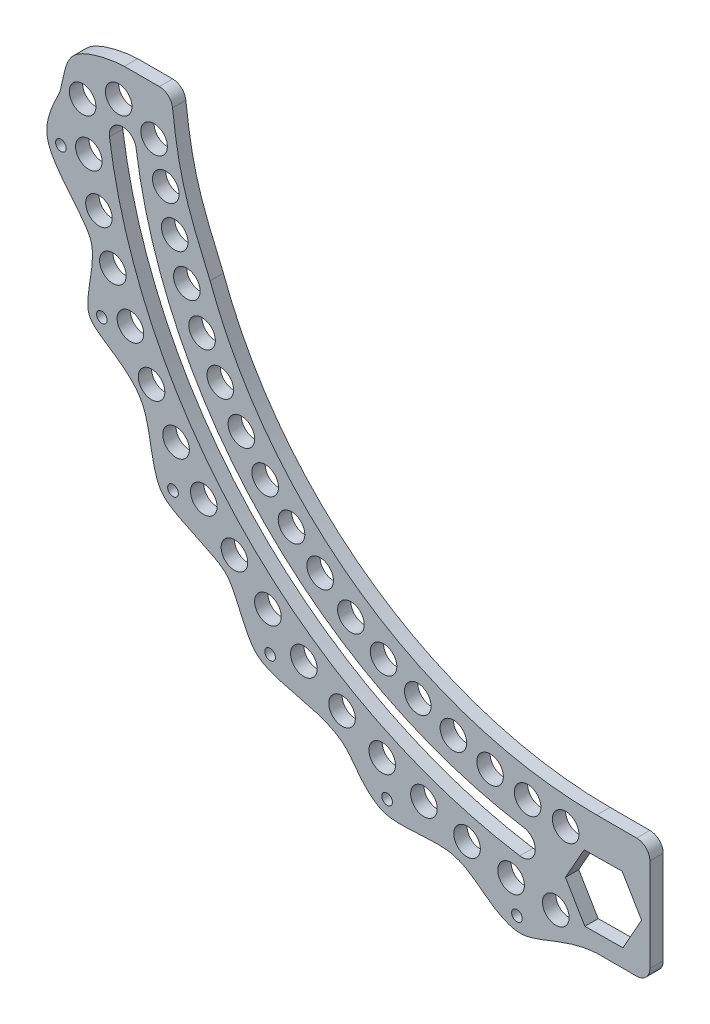
SolidWorks part; units mm, degrees
material "6061-T6 (SS)"
ref_plane "Front Plane" through (0, 0, 0) normal (0, 0, 1) x (1, 0, 0)
ref_plane "Top Plane" through (0, 0, 0) normal (0, 1, 0) x (1, 0, 0)
ref_plane "Right Plane" through (0, 0, 0) normal (1, 0, 0) x (0, 0, -1)
sketch "Layout" plane through (0, 0, 0) normal (0, 0, 1) x (1, 0, 0)
  line L0 (0, 0) -> (-76.2, 0) construction
  line L1 (-76.2, 0) -> (-203.2, 0) construction
  line L2 (-203.2, 0) -> (-254, 0) construction
  dimension "D1" = 76.2
  dimension "D2" = 127
  dimension "D3" = 50.8
sketch "Sketch1" plane through (0, 0, 0) normal (0, 0, 1) x (1, 0, 0)
  line L0 (0, 0) -> (-203.2, 0) construction
  line L1 (0, 0) -> (0, -203.2) construction
  line L2 (0, -203.2) -> (25.4, -203.2)
  line L3 (0, -254) -> (25.4, -254)
  line L4 (-254, 0) -> (-203.2, 0)
  line L5 (25.4, -203.2) -> (25.4, -254)
  arc A0 (-203.2, 0) -> (0, -203.2) centre (0, 0) ccw
  arc A1 (-254, 0) -> (0, -254) centre (0, 0) ccw
  dimension "D1" = 50.8
  dimension "D2" = 25.4
  dimension "D3" = 203.2
extrude "Boss-Extrude1" add sketch "Sketch1" along normal blind 6.35
ref_plane "Mid_Plane" through (0, 0, 3.175) normal (0, 0, 1) x (1, 0, 0)
sketch "Sketch2" plane through (0, 0, 6.35) normal (0, 0, 1) x (1, 0, 0)
  line L0 (0, 0) -> (-229.3095, 0) construction
  line L1 (0, 0) -> (-226.3753, -31.815) construction
  line L2 (0, 0) -> (-35.7609, -225.7856) construction
  arc A0 (-226.3753, -31.815) -> (-35.7609, -225.7856) centre (0, 0) ccw construction
  arc A1 (-226.3753, -31.815) -> (-35.7609, -225.7856) centre (0, 0) ccw construction
  arc A2 (-232.7264, -32.7076) -> (-36.7642, -232.1201) centre (0, 0) ccw
  arc A3 (-220.0242, -30.9224) -> (-34.7576, -219.451) centre (0, 0) ccw
  arc A4 (-220.0242, -30.9224) -> (-232.7264, -32.7076) centre (-226.3753, -31.815) ccw
  arc A5 (-36.7642, -232.1201) -> (-34.7576, -219.451) centre (-35.7609, -225.7856) ccw
  point P5 (-163.0491, -160.2279)
  dimension "D1" = 73
  dimension "D3" = 12.827
  dimension "D4" = 228.6
  dimension "D2" = 8
extrude "Cut-Extrude1" cut sketch "Sketch2" against normal up to next
fillet "Fillet1" [suppressed] radius 12.7
ref_point "Mid_Point"
sketch "Sketch4" plane through (0, 0, 0) normal (0, 0, -1) x (-1, 0, 0)
  line L0 (254, 0) -> (266.7, 0)
  line L1 (0, -254) -> (0, -266.7)
  arc A0 (0, -254) -> (254, 0) centre (0, 0) ccw construction
  arc A1 (0, -254) -> (254, 0) centre (0, 0) ccw
  arc A2 (0, -266.7) -> (266.7, 0) centre (0, 0) ccw
extrude "Boss-Extrude3" add sketch "Sketch4" against normal up to surface (6.35 mm away) up to face at (-145.6981, -143.1771, 6.35)
fillet "Fillet2" radius 12.7 2 edges at (-266.7, 0, 3.175) (0, -266.7, 3.175)
sketch "Sketch5" plane through (0, 0, 0) normal (0, 0, -1) x (-1, 0, 0)
  line L0 (2.758, -261.6055) -> (3.6103, -266.6756)
  line L1 (0, 0) -> (306.4939, -16.1536) construction
  line L2 (0, -261.62) -> (0.7987, -266.6988)
  line L3 (0, -261.62) -> (-1.3603, -266.6965)
  line L4 (2.758, -261.6055) -> (1.4514, -266.6961)
  line L5 (5.5157, -261.5618) -> (6.4214, -266.6227)
  line L6 (5.5157, -261.5618) -> (4.2628, -266.6659)
  line L7 (8.2728, -261.4892) -> (9.2318, -266.5402)
  line L8 (8.2728, -261.4892) -> (7.0738, -266.6062)
  line L9 (11.029, -261.3874) -> (12.0411, -266.428)
  line L10 (11.029, -261.3874) -> (9.884, -266.5168)
  line L11 (13.7839, -261.2566) -> (14.8492, -266.2863)
  line L12 (13.7839, -261.2566) -> (12.693, -266.3978)
  line L13 (16.5374, -261.0968) -> (17.6555, -266.115)
  line L14 (16.5374, -261.0968) -> (15.5007, -266.2492)
  line L15 (19.2889, -260.908) -> (20.46, -265.914)
  line L16 (19.2889, -260.908) -> (18.3067, -266.071)
  line L17 (22.0384, -260.6901) -> (23.2621, -265.6836)
  line L18 (22.0384, -260.6901) -> (21.1106, -265.8632)
  line L19 (24.7854, -260.4433) -> (26.0617, -265.4236)
  line L20 (24.7854, -260.4433) -> (23.9122, -265.6259)
  line L21 (27.5296, -260.1675) -> (28.8583, -265.1341)
  line L22 (27.5296, -260.1675) -> (26.7111, -265.359)
  line L23 (30.2708, -259.8629) -> (31.6518, -264.8151)
  line L24 (30.2708, -259.8629) -> (29.507, -265.0627)
  line L25 (33.0086, -259.5293) -> (34.4417, -264.4667)
  line L26 (33.0086, -259.5293) -> (32.2997, -264.7369)
  line L27 (35.7427, -259.1669) -> (37.2278, -264.089)
  line L28 (35.7427, -259.1669) -> (35.0888, -264.3817)
  line L29 (38.4729, -258.7757) -> (40.0098, -263.6818)
  line L30 (38.4729, -258.7757) -> (37.874, -263.9971)
  line L31 (41.1988, -258.3557) -> (42.7873, -263.2454)
  line L32 (41.1988, -258.3557) -> (40.6549, -263.5831)
  line L33 (43.9201, -257.9071) -> (45.5601, -262.7797)
  line L34 (43.9201, -257.9071) -> (43.4314, -263.1399)
  line L35 (46.6365, -257.4297) -> (48.3278, -262.2848)
  line L36 (46.6365, -257.4297) -> (46.203, -262.6674)
  line L37 (49.3478, -256.9238) -> (51.0902, -261.7607)
  line L38 (49.3478, -256.9238) -> (48.9695, -262.1657)
  line L39 (52.0535, -256.3893) -> (53.8468, -261.2076)
  line L40 (52.0535, -256.3893) -> (51.7305, -261.6349)
  line L41 (54.7535, -255.8263) -> (56.5975, -260.6254)
  line L42 (54.7535, -255.8263) -> (54.4858, -261.0751)
  line L43 (57.4474, -255.2348) -> (59.3419, -260.0143)
  line L44 (57.4474, -255.2348) -> (57.2351, -260.4862)
  line L45 (60.1349, -254.615) -> (62.0797, -259.3743)
  line L46 (60.1349, -254.615) -> (59.978, -259.8683)
  line L47 (62.8157, -253.9669) -> (64.8106, -258.7054)
  line L48 (62.8157, -253.9669) -> (62.7142, -259.2216)
  line L49 (65.4896, -253.2906) -> (67.5342, -258.0078)
  line L50 (65.4896, -253.2906) -> (65.4434, -258.546)
  line L51 (68.1561, -252.5862) -> (70.2504, -257.2815)
  line L52 (68.1561, -252.5862) -> (68.1654, -257.8418)
  line L53 (70.8151, -251.8536) -> (72.9588, -256.5266)
  line L54 (70.8151, -251.8536) -> (70.8798, -257.1088)
  line L55 (73.4663, -251.0931) -> (75.6591, -255.7432)
  line L56 (73.4663, -251.0931) -> (73.5863, -256.3473)
  line L57 (76.1092, -250.3046) -> (78.3509, -254.9314)
  line L58 (76.1092, -250.3046) -> (76.2846, -255.5573)
  line L59 (78.7437, -249.4884) -> (81.0341, -254.0913)
  line L60 (78.7437, -249.4884) -> (78.9745, -254.7389)
  line L61 (81.3695, -248.6444) -> (83.7082, -253.2229)
  line L62 (81.3695, -248.6444) -> (81.6556, -253.8922)
  line L63 (83.9862, -247.7728) -> (86.373, -252.3263)
  line L64 (83.9862, -247.7728) -> (84.3276, -253.0173)
  line L65 (86.5935, -246.8736) -> (89.0283, -251.4018)
  line L66 (86.5935, -246.8736) -> (86.9902, -252.1142)
  line L67 (89.1913, -245.947) -> (91.6736, -250.4493)
  line L68 (89.1913, -245.947) -> (89.6432, -251.1832)
  line L69 (91.7791, -244.9931) -> (94.3088, -249.4689)
  line L70 (91.7791, -244.9931) -> (92.2862, -250.2242)
  line L71 (94.3567, -244.0119) -> (96.9335, -248.4608)
  line L72 (94.3567, -244.0119) -> (94.919, -249.2374)
  line L73 (96.9239, -243.0037) -> (99.5474, -247.4252)
  line L74 (96.9239, -243.0037) -> (97.5412, -248.2229)
  line L75 (99.4803, -241.9684) -> (102.1502, -246.362)
  line L76 (99.4803, -241.9684) -> (100.1525, -247.1808)
  line L77 (102.0256, -240.9062) -> (104.7417, -245.2714)
  line L78 (102.0256, -240.9062) -> (102.7528, -246.1113)
  line L79 (104.5596, -239.8173) -> (107.3215, -244.1536)
  line L80 (104.5596, -239.8173) -> (105.3416, -245.0144)
  line L81 (107.0819, -238.7017) -> (109.8895, -243.0086)
  line L82 (107.0819, -238.7017) -> (107.9187, -243.8902)
  line L83 (109.5924, -237.5595) -> (112.4452, -241.8367)
  line L84 (109.5924, -237.5595) -> (110.4838, -242.739)
  line L85 (112.0907, -236.391) -> (114.9884, -240.6378)
  line L86 (112.0907, -236.391) -> (113.0366, -241.5608)
  line L87 (114.5765, -235.1962) -> (117.5188, -239.4122)
  line L88 (114.5765, -235.1962) -> (115.5769, -240.3557)
  line L89 (117.0496, -233.9753) -> (120.0362, -238.16)
  line L90 (117.0496, -233.9753) -> (118.1043, -239.124)
  line L91 (119.5096, -232.7283) -> (122.5402, -236.8814)
  line L92 (119.5096, -232.7283) -> (120.6186, -237.8656)
  line L93 (121.9564, -231.4555) -> (125.0306, -235.5764)
  line L94 (121.9564, -231.4555) -> (123.1195, -236.5808)
  line L95 (124.3897, -230.157) -> (127.5071, -234.2452)
  line L96 (124.3897, -230.157) -> (125.6067, -235.2697)
  line L97 (126.8091, -228.8329) -> (129.9695, -232.888)
  line L98 (126.8091, -228.8329) -> (128.0799, -233.9325)
  line L99 (129.2144, -227.4833) -> (132.4174, -231.5049)
  line L100 (129.2144, -227.4833) -> (130.539, -232.5693)
  line L101 (131.6054, -226.1085) -> (134.8505, -230.0961)
  line L102 (131.6054, -226.1085) -> (132.9835, -231.1802)
  line L103 (133.9817, -224.7085) -> (137.2687, -228.6617)
  line L104 (133.9817, -224.7085) -> (135.4132, -229.7654)
  line L105 (136.3432, -223.2836) -> (139.6717, -227.2019)
  line L106 (136.3432, -223.2836) -> (137.8279, -228.3251)
  line L107 (138.6895, -221.8339) -> (142.0591, -225.7169)
  line L108 (138.6895, -221.8339) -> (140.2272, -226.8595)
  line L109 (141.0203, -220.3595) -> (144.4307, -224.2067)
  line L110 (141.0203, -220.3595) -> (142.611, -225.3686)
  line L111 (143.3355, -218.8606) -> (146.7863, -222.6717)
  line L112 (143.3355, -218.8606) -> (144.9789, -223.8526)
  line L113 (145.6348, -217.3374) -> (149.1256, -221.1119)
  line L114 (145.6348, -217.3374) -> (147.3307, -222.3118)
  line L115 (147.9179, -215.79) -> (151.4482, -219.5275)
  line L116 (147.9179, -215.79) -> (149.6662, -220.7463)
  line L117 (150.1846, -214.2186) -> (153.7541, -217.9187)
  line L118 (150.1846, -214.2186) -> (151.985, -219.1562)
  line L119 (152.4345, -212.6235) -> (156.0429, -216.2857)
  line L120 (152.4345, -212.6235) -> (154.2869, -217.5418)
  line L121 (154.6675, -211.0047) -> (158.3143, -214.6287)
  line L122 (154.6675, -211.0047) -> (156.5717, -215.9032)
  line L123 (156.8834, -209.3624) -> (160.5681, -212.9478)
  line L124 (156.8834, -209.3624) -> (158.839, -214.2407)
  line L125 (159.0818, -207.6969) -> (162.8041, -211.2432)
  line L126 (159.0818, -207.6969) -> (161.0887, -212.5543)
  line L127 (161.2625, -206.0083) -> (165.022, -209.5152)
  line L128 (161.2625, -206.0083) -> (163.3205, -210.8442)
  line L129 (163.4253, -204.2969) -> (167.2216, -207.7639)
  line L130 (163.4253, -204.2969) -> (165.5342, -209.1108)
  line L131 (165.5699, -202.5627) -> (169.4025, -205.9895)
  line L132 (165.5699, -202.5627) -> (167.7295, -207.3541)
  line L133 (167.6961, -200.806) -> (171.5647, -204.1922)
  line L134 (167.6961, -200.806) -> (169.9061, -205.5744)
  line L135 (169.8037, -199.0269) -> (173.7077, -202.3722)
  line L136 (169.8037, -199.0269) -> (172.0638, -203.7718)
  line L137 (171.8924, -197.2258) -> (175.8315, -200.5297)
  line L138 (171.8924, -197.2258) -> (174.2024, -201.9465)
  line L139 (173.962, -195.4027) -> (177.9357, -198.665)
  line L140 (173.962, -195.4027) -> (176.3217, -200.0989)
  line L141 (176.0123, -193.558) -> (180.0202, -196.7781)
  line L142 (176.0123, -193.558) -> (178.4213, -198.229)
  line L143 (178.043, -191.6917) -> (182.0846, -194.8694)
  line L144 (178.043, -191.6917) -> (180.5012, -196.337)
  line L145 (180.054, -189.8041) -> (184.1288, -192.939)
  line L146 (180.054, -189.8041) -> (182.5609, -194.4232)
  line L147 (182.0449, -187.8954) -> (186.1526, -190.9872)
  line L148 (182.0449, -187.8954) -> (184.6004, -192.4879)
  line L149 (184.0156, -185.9658) -> (188.1556, -189.0141)
  line L150 (184.0156, -185.9658) -> (186.6194, -190.5311)
  line L151 (185.9658, -184.0156) -> (190.1378, -187.0201)
  line L152 (185.9658, -184.0156) -> (188.6176, -188.5532)
  line L153 (187.8954, -182.0449) -> (192.0988, -185.0053)
  line L154 (187.8954, -182.0449) -> (190.5948, -186.5543)
  line L155 (189.8041, -180.054) -> (194.0384, -182.9699)
  line L156 (189.8041, -180.054) -> (192.5509, -184.5346)
  line L157 (191.6917, -178.043) -> (195.9565, -180.9141)
  line L158 (191.6917, -178.043) -> (194.4856, -182.4945)
  line L159 (193.558, -176.0123) -> (197.8529, -178.8383)
  line L160 (193.558, -176.0123) -> (196.3987, -180.4341)
  line L161 (195.4027, -173.962) -> (199.7272, -176.7426)
  line L162 (195.4027, -173.962) -> (198.2899, -178.3536)
  line L163 (197.2258, -171.8924) -> (201.5793, -174.6272)
  line L164 (197.2258, -171.8924) -> (200.1591, -176.2533)
  line L165 (199.0269, -169.8037) -> (203.4091, -172.4925)
  line L166 (199.0269, -169.8037) -> (202.006, -174.1334)
  line L167 (200.806, -167.6961) -> (205.2162, -170.3385)
  line L168 (200.806, -167.6961) -> (203.8305, -171.9942)
  line L169 (202.5627, -165.5699) -> (207.0005, -168.1656)
  line L170 (202.5627, -165.5699) -> (205.6324, -169.8358)
  line L171 (204.2969, -163.4253) -> (208.7618, -165.9741)
  line L172 (204.2969, -163.4253) -> (207.4114, -167.6586)
  line L173 (206.0083, -161.2625) -> (210.4999, -163.7641)
  line L174 (206.0083, -161.2625) -> (209.1673, -165.4628)
  line L175 (207.6969, -159.0818) -> (212.2146, -161.5359)
  line L176 (207.6969, -159.0818) -> (210.9, -163.2485)
  line L177 (209.3624, -156.8834) -> (213.9058, -159.2897)
  line L178 (209.3624, -156.8834) -> (212.6093, -161.0161)
  line L179 (211.0047, -154.6675) -> (215.5731, -157.0259)
  line L180 (211.0047, -154.6675) -> (214.2949, -158.7658)
  line L181 (212.6235, -152.4345) -> (217.2165, -154.7446)
  line L182 (212.6235, -152.4345) -> (215.9567, -156.4979)
  line L183 (214.2186, -150.1846) -> (218.8358, -152.446)
  line L184 (214.2186, -150.1846) -> (217.5945, -154.2126)
  line L185 (215.79, -147.9179) -> (220.4307, -150.1306)
  line L186 (215.79, -147.9179) -> (219.2081, -151.9101)
  line L187 (217.3374, -145.6348) -> (222.0011, -147.7985)
  line L188 (217.3374, -145.6348) -> (220.7974, -149.5908)
  line L189 (218.8606, -143.3355) -> (223.5469, -145.4499)
  line L190 (218.8606, -143.3355) -> (222.3621, -147.2548)
  line L191 (220.3595, -141.0203) -> (225.0678, -143.0852)
  line L192 (220.3595, -141.0203) -> (223.9021, -144.9024)
  line L193 (221.8339, -138.6895) -> (226.5637, -140.7045)
  line L194 (221.8339, -138.6895) -> (225.4173, -142.534)
  line L195 (223.2836, -136.3432) -> (228.0345, -138.3083)
  line L196 (223.2836, -136.3432) -> (226.9074, -140.1497)
  line L197 (224.7085, -133.9817) -> (229.4798, -135.8966)
  line L198 (224.7085, -133.9817) -> (228.3722, -137.7499)
  line L199 (226.1085, -131.6054) -> (230.8997, -133.4699)
  line L200 (226.1085, -131.6054) -> (229.8117, -135.3347)
  line L201 (227.4833, -129.2144) -> (232.2939, -131.0283)
  line L202 (227.4833, -129.2144) -> (231.2256, -132.9045)
  line L203 (228.8329, -126.8091) -> (233.6623, -128.5722)
  line L204 (228.8329, -126.8091) -> (232.6139, -130.4595)
  line L205 (230.157, -124.3897) -> (235.0048, -126.1017)
  line L206 (230.157, -124.3897) -> (233.9762, -128)
  line L207 (231.4555, -121.9564) -> (236.3211, -123.6173)
  line L208 (231.4555, -121.9564) -> (235.3126, -125.5263)
  line L209 (232.7283, -119.5096) -> (237.6111, -121.1191)
  line L210 (232.7283, -119.5096) -> (236.6229, -123.0387)
  line L211 (233.9753, -117.0496) -> (238.8748, -118.6075)
  line L212 (233.9753, -117.0496) -> (237.9068, -120.5373)
  line L213 (235.1962, -114.5765) -> (240.1119, -116.0827)
  line L214 (235.1962, -114.5765) -> (239.1643, -118.0226)
  line L215 (236.391, -112.0907) -> (241.3223, -113.5449)
  line L216 (236.391, -112.0907) -> (240.3952, -115.4948)
  line L217 (237.5595, -109.5924) -> (242.5059, -110.9946)
  line L218 (237.5595, -109.5924) -> (241.5994, -112.9541)
  line L219 (238.7017, -107.0819) -> (243.6625, -108.4319)
  line L220 (238.7017, -107.0819) -> (242.7767, -110.4009)
  line L221 (239.8173, -104.5596) -> (244.792, -105.8572)
  line L222 (239.8173, -104.5596) -> (243.9271, -107.8353)
  line L223 (240.9062, -102.0256) -> (245.8944, -103.2707)
  line L224 (240.9062, -102.0256) -> (245.0503, -105.2579)
  line L225 (241.9684, -99.4803) -> (246.9694, -100.6727)
  line L226 (241.9684, -99.4803) -> (246.1464, -102.6687)
  line L227 (243.0037, -96.9239) -> (248.017, -98.0636)
  line L228 (243.0037, -96.9239) -> (247.215, -100.0681)
  line L229 (244.0119, -94.3567) -> (249.037, -95.4435)
  line L230 (244.0119, -94.3567) -> (248.2562, -97.4564)
  line L231 (244.9931, -91.7791) -> (250.0293, -92.8128)
  line L232 (244.9931, -91.7791) -> (249.2698, -94.8338)
  line L233 (245.947, -89.1913) -> (250.9939, -90.1718)
  line L234 (245.947, -89.1913) -> (250.2557, -92.2007)
  line L235 (246.8736, -86.5935) -> (251.9305, -87.5208)
  line L236 (246.8736, -86.5935) -> (251.2138, -89.5574)
  line L237 (247.7728, -83.9862) -> (252.8392, -84.8601)
  line L238 (247.7728, -83.9862) -> (252.1439, -86.9041)
  line L239 (248.6444, -81.3695) -> (253.7197, -82.1899)
  line L240 (248.6444, -81.3695) -> (253.0461, -84.2412)
  line L241 (249.4884, -78.7437) -> (254.5721, -79.5107)
  line L242 (249.4884, -78.7437) -> (253.9201, -81.5689)
  line L243 (250.3046, -76.1092) -> (255.3961, -76.8225)
  line L244 (250.3046, -76.1092) -> (254.7659, -78.8875)
  line L245 (251.0931, -73.4663) -> (256.1918, -74.1258)
  line L246 (251.0931, -73.4663) -> (255.5834, -76.1973)
  line L247 (251.8536, -70.8151) -> (256.959, -71.4209)
  line L248 (251.8536, -70.8151) -> (256.3724, -73.4987)
  line L249 (252.5862, -68.1561) -> (257.6977, -68.7081)
  line L250 (252.5862, -68.1561) -> (257.133, -70.7919)
  line L251 (253.2906, -65.4896) -> (258.4077, -65.9876)
  line L252 (253.2906, -65.4896) -> (257.865, -68.0773)
  line L253 (253.9669, -62.8157) -> (259.089, -63.2598)
  line L254 (253.9669, -62.8157) -> (258.5684, -65.3551)
  line L255 (254.615, -60.1349) -> (259.7415, -60.5249)
  line L256 (254.615, -60.1349) -> (259.243, -62.6256)
  line L257 (255.2348, -57.4474) -> (260.3651, -57.7834)
  line L258 (255.2348, -57.4474) -> (259.8888, -59.8892)
  line L259 (255.8263, -54.7535) -> (260.9598, -55.0354)
  line L260 (255.8263, -54.7535) -> (260.5057, -57.1461)
  line L261 (256.3893, -52.0535) -> (261.5254, -52.2813)
  line L262 (256.3893, -52.0535) -> (261.0937, -54.3966)
  line L263 (256.9238, -49.3478) -> (262.0621, -49.5213)
  line L264 (256.9238, -49.3478) -> (261.6526, -51.6412)
  line L265 (257.4297, -46.6365) -> (262.5696, -46.7559)
  line L266 (257.4297, -46.6365) -> (262.1825, -48.8799)
  line L267 (257.9071, -43.9201) -> (263.0479, -43.9853)
  line L268 (257.9071, -43.9201) -> (262.6832, -46.1133)
  line L269 (258.3557, -41.1988) -> (263.497, -41.2098)
  line L270 (258.3557, -41.1988) -> (263.1547, -43.3415)
  line L271 (258.7757, -38.4729) -> (263.9167, -38.4297)
  line L272 (258.7757, -38.4729) -> (263.597, -40.5649)
  line L273 (259.1669, -35.7427) -> (264.3072, -35.6453)
  line L274 (259.1669, -35.7427) -> (264.01, -37.7838)
  line L275 (259.5293, -33.0086) -> (264.6683, -32.857)
  line L276 (259.5293, -33.0086) -> (264.3936, -34.9985)
  line L277 (259.8629, -30.2708) -> (265, -30.065)
  line L278 (259.8629, -30.2708) -> (264.7479, -32.2093)
  line L279 (260.1675, -27.5296) -> (265.3022, -27.2697)
  line L280 (260.1675, -27.5296) -> (265.0727, -29.4165)
  line L281 (260.4433, -24.7854) -> (265.5749, -24.4714)
  line L282 (260.4433, -24.7854) -> (265.3681, -26.6204)
  line L283 (260.6901, -22.0384) -> (265.8181, -21.6703)
  line L284 (260.6901, -22.0384) -> (265.634, -23.8214)
  line L285 (260.908, -19.2889) -> (266.0318, -18.8668)
  line L286 (260.908, -19.2889) -> (265.8704, -21.0198)
  line L287 (261.0968, -16.5374) -> (266.2159, -16.0612)
  line L288 (261.0968, -16.5374) -> (266.0772, -18.2158)
  line L289 (261.2566, -13.7839) -> (266.3705, -13.2539)
  line L290 (261.2566, -13.7839) -> (266.2544, -15.4098)
  line L291 (261.3874, -11.029) -> (266.4954, -10.4451)
  line L292 (261.3874, -11.029) -> (266.4021, -12.602)
  line L301 (0, 0) -> (0, -261.62) construction
  arc A0 (13.3308, -266.3666) -> (266.3664, -13.335) centre (0, 0) ccw construction
  arc A1 (-1.3603, -266.6965) -> (0.7987, -266.6988) centre (0, 0) ccw
  arc A2 (1.4514, -266.6961) -> (3.6103, -266.6756) centre (0, 0) ccw
  arc A3 (4.2628, -266.6659) -> (6.4214, -266.6227) centre (0, 0) ccw
  arc A4 (7.0738, -266.6062) -> (9.2318, -266.5402) centre (0, 0) ccw
  arc A5 (9.884, -266.5168) -> (12.0411, -266.428) centre (0, 0) ccw
  arc A6 (12.693, -266.3978) -> (14.8492, -266.2863) centre (0, 0) ccw
  arc A7 (15.5007, -266.2492) -> (17.6555, -266.115) centre (0, 0) ccw
  arc A8 (18.3067, -266.071) -> (20.46, -265.914) centre (0, 0) ccw
  arc A9 (21.1106, -265.8632) -> (23.2621, -265.6836) centre (0, 0) ccw
  arc A10 (23.9122, -265.6259) -> (26.0617, -265.4236) centre (0, 0) ccw
  arc A11 (26.7111, -265.359) -> (28.8583, -265.1341) centre (0, 0) ccw
  arc A12 (29.507, -265.0627) -> (31.6518, -264.8151) centre (0, 0) ccw
  arc A13 (32.2997, -264.7369) -> (34.4417, -264.4667) centre (0, 0) ccw
  arc A14 (35.0888, -264.3817) -> (37.2278, -264.089) centre (0, 0) ccw
  arc A15 (37.874, -263.9971) -> (40.0098, -263.6818) centre (0, 0) ccw
  arc A16 (40.6549, -263.5831) -> (42.7873, -263.2454) centre (0, 0) ccw
  arc A17 (43.4314, -263.1399) -> (45.5601, -262.7797) centre (0, 0) ccw
  arc A18 (46.203, -262.6674) -> (48.3278, -262.2848) centre (0, 0) ccw
  arc A19 (48.9695, -262.1657) -> (51.0902, -261.7607) centre (0, 0) ccw
  arc A20 (51.7305, -261.6349) -> (53.8468, -261.2076) centre (0, 0) ccw
  arc A21 (54.4858, -261.0751) -> (56.5975, -260.6254) centre (0, 0) ccw
  arc A22 (57.2351, -260.4862) -> (59.3419, -260.0143) centre (0, 0) ccw
  arc A23 (59.978, -259.8683) -> (62.0797, -259.3743) centre (0, 0) ccw
  arc A24 (62.7142, -259.2216) -> (64.8106, -258.7054) centre (0, 0) ccw
  arc A25 (65.4434, -258.546) -> (67.5342, -258.0078) centre (0, 0) ccw
  arc A26 (68.1654, -257.8418) -> (70.2504, -257.2815) centre (0, 0) ccw
  arc A27 (70.8798, -257.1088) -> (72.9588, -256.5266) centre (0, 0) ccw
  arc A28 (73.5863, -256.3473) -> (75.6591, -255.7432) centre (0, 0) ccw
  arc A29 (76.2846, -255.5573) -> (78.3509, -254.9314) centre (0, 0) ccw
  arc A30 (78.9745, -254.7389) -> (81.0341, -254.0913) centre (0, 0) ccw
  arc A31 (81.6556, -253.8922) -> (83.7082, -253.2229) centre (0, 0) ccw
  arc A32 (84.3276, -253.0173) -> (86.373, -252.3263) centre (0, 0) ccw
  arc A33 (86.9902, -252.1142) -> (89.0283, -251.4018) centre (0, 0) ccw
  arc A34 (89.6432, -251.1832) -> (91.6736, -250.4493) centre (0, 0) ccw
  arc A35 (92.2862, -250.2242) -> (94.3088, -249.4689) centre (0, 0) ccw
  arc A36 (94.919, -249.2374) -> (96.9335, -248.4608) centre (0, 0) ccw
  arc A37 (97.5412, -248.2229) -> (99.5474, -247.4252) centre (0, 0) ccw
  arc A38 (100.1525, -247.1808) -> (102.1502, -246.362) centre (0, 0) ccw
  arc A39 (102.7528, -246.1113) -> (104.7417, -245.2714) centre (0, 0) ccw
  arc A40 (105.3416, -245.0144) -> (107.3215, -244.1536) centre (0, 0) ccw
  arc A41 (107.9187, -243.8902) -> (109.8895, -243.0086) centre (0, 0) ccw
  arc A42 (110.4838, -242.739) -> (112.4452, -241.8367) centre (0, 0) ccw
  arc A43 (113.0366, -241.5608) -> (114.9884, -240.6378) centre (0, 0) ccw
  arc A44 (115.5769, -240.3557) -> (117.5188, -239.4122) centre (0, 0) ccw
  arc A45 (118.1043, -239.124) -> (120.0362, -238.16) centre (0, 0) ccw
  arc A46 (120.6186, -237.8656) -> (122.5402, -236.8814) centre (0, 0) ccw
  arc A47 (123.1195, -236.5808) -> (125.0306, -235.5764) centre (0, 0) ccw
  arc A48 (125.6067, -235.2697) -> (127.5071, -234.2452) centre (0, 0) ccw
  arc A49 (128.0799, -233.9325) -> (129.9695, -232.888) centre (0, 0) ccw
  arc A50 (130.539, -232.5693) -> (132.4174, -231.5049) centre (0, 0) ccw
  arc A51 (132.9835, -231.1802) -> (134.8505, -230.0961) centre (0, 0) ccw
  arc A52 (135.4132, -229.7654) -> (137.2687, -228.6617) centre (0, 0) ccw
  arc A53 (137.8279, -228.3251) -> (139.6717, -227.2019) centre (0, 0) ccw
  arc A54 (140.2272, -226.8595) -> (142.0591, -225.7169) centre (0, 0) ccw
  arc A55 (142.611, -225.3686) -> (144.4307, -224.2067) centre (0, 0) ccw
  arc A56 (144.9789, -223.8526) -> (146.7863, -222.6717) centre (0, 0) ccw
  arc A57 (147.3307, -222.3118) -> (149.1256, -221.1119) centre (0, 0) ccw
  arc A58 (149.6662, -220.7463) -> (151.4482, -219.5275) centre (0, 0) ccw
  arc A59 (151.985, -219.1562) -> (153.7541, -217.9187) centre (0, 0) ccw
  arc A60 (154.2869, -217.5418) -> (156.0429, -216.2857) centre (0, 0) ccw
  arc A61 (156.5717, -215.9032) -> (158.3143, -214.6287) centre (0, 0) ccw
  arc A62 (158.839, -214.2407) -> (160.5681, -212.9478) centre (0, 0) ccw
  arc A63 (161.0887, -212.5543) -> (162.8041, -211.2432) centre (0, 0) ccw
  arc A64 (163.3205, -210.8442) -> (165.022, -209.5152) centre (0, 0) ccw
  arc A65 (165.5342, -209.1108) -> (167.2216, -207.7639) centre (0, 0) ccw
  arc A66 (167.7295, -207.3541) -> (169.4025, -205.9895) centre (0, 0) ccw
  arc A67 (169.9061, -205.5744) -> (171.5647, -204.1922) centre (0, 0) ccw
  arc A68 (172.0638, -203.7718) -> (173.7077, -202.3722) centre (0, 0) ccw
  arc A69 (174.2024, -201.9465) -> (175.8315, -200.5297) centre (0, 0) ccw
  arc A70 (176.3217, -200.0989) -> (177.9357, -198.665) centre (0, 0) ccw
  arc A71 (178.4213, -198.229) -> (180.0202, -196.7781) centre (0, 0) ccw
  arc A72 (180.5012, -196.337) -> (182.0846, -194.8694) centre (0, 0) ccw
  arc A73 (182.5609, -194.4232) -> (184.1288, -192.939) centre (0, 0) ccw
  arc A74 (184.6004, -192.4879) -> (186.1526, -190.9872) centre (0, 0) ccw
  arc A75 (186.6194, -190.5311) -> (188.1556, -189.0141) centre (0, 0) ccw
  arc A76 (188.6176, -188.5532) -> (190.1378, -187.0201) centre (0, 0) ccw
  arc A77 (190.5948, -186.5543) -> (192.0988, -185.0053) centre (0, 0) ccw
  arc A78 (192.5509, -184.5346) -> (194.0384, -182.9699) centre (0, 0) ccw
  arc A79 (194.4856, -182.4945) -> (195.9565, -180.9141) centre (0, 0) ccw
  arc A80 (196.3987, -180.4341) -> (197.8529, -178.8383) centre (0, 0) ccw
  arc A81 (198.2899, -178.3536) -> (199.7272, -176.7426) centre (0, 0) ccw
  arc A82 (200.1591, -176.2533) -> (201.5793, -174.6272) centre (0, 0) ccw
  arc A83 (202.006, -174.1334) -> (203.4091, -172.4925) centre (0, 0) ccw
  arc A84 (203.8305, -171.9942) -> (205.2162, -170.3385) centre (0, 0) ccw
  arc A85 (205.6324, -169.8358) -> (207.0005, -168.1656) centre (0, 0) ccw
  arc A86 (207.4114, -167.6586) -> (208.7618, -165.9741) centre (0, 0) ccw
  arc A87 (209.1673, -165.4628) -> (210.4999, -163.7641) centre (0, 0) ccw
  arc A88 (210.9, -163.2485) -> (212.2146, -161.5359) centre (0, 0) ccw
  arc A89 (212.6093, -161.0161) -> (213.9058, -159.2897) centre (0, 0) ccw
  arc A90 (214.2949, -158.7658) -> (215.5731, -157.0259) centre (0, 0) ccw
  arc A91 (215.9567, -156.4979) -> (217.2165, -154.7446) centre (0, 0) ccw
  arc A92 (217.5945, -154.2126) -> (218.8358, -152.446) centre (0, 0) ccw
  arc A93 (219.2081, -151.9101) -> (220.4307, -150.1306) centre (0, 0) ccw
  arc A94 (220.7974, -149.5908) -> (222.0011, -147.7985) centre (0, 0) ccw
  arc A95 (222.3621, -147.2548) -> (223.5469, -145.4499) centre (0, 0) ccw
  arc A96 (223.9021, -144.9024) -> (225.0678, -143.0852) centre (0, 0) ccw
  arc A97 (225.4173, -142.534) -> (226.5637, -140.7045) centre (0, 0) ccw
  arc A98 (226.9074, -140.1497) -> (228.0345, -138.3083) centre (0, 0) ccw
  arc A99 (228.3722, -137.7499) -> (229.4798, -135.8966) centre (0, 0) ccw
  arc A100 (229.8117, -135.3347) -> (230.8997, -133.4699) centre (0, 0) ccw
  arc A101 (231.2256, -132.9045) -> (232.2939, -131.0283) centre (0, 0) ccw
  arc A102 (232.6139, -130.4595) -> (233.6623, -128.5722) centre (0, 0) ccw
  arc A103 (233.9762, -128) -> (235.0048, -126.1017) centre (0, 0) ccw
  arc A104 (235.3126, -125.5263) -> (236.3211, -123.6173) centre (0, 0) ccw
  arc A105 (236.6229, -123.0387) -> (237.6111, -121.1191) centre (0, 0) ccw
  arc A106 (237.9068, -120.5373) -> (238.8748, -118.6075) centre (0, 0) ccw
  arc A107 (239.1643, -118.0226) -> (240.1119, -116.0827) centre (0, 0) ccw
  arc A108 (240.3952, -115.4948) -> (241.3223, -113.5449) centre (0, 0) ccw
  arc A109 (241.5994, -112.9541) -> (242.5059, -110.9946) centre (0, 0) ccw
  arc A110 (242.7767, -110.4009) -> (243.6625, -108.4319) centre (0, 0) ccw
  arc A111 (243.9271, -107.8353) -> (244.792, -105.8572) centre (0, 0) ccw
  arc A112 (245.0503, -105.2579) -> (245.8944, -103.2707) centre (0, 0) ccw
  arc A113 (246.1464, -102.6687) -> (246.9694, -100.6727) centre (0, 0) ccw
  arc A114 (247.215, -100.0681) -> (248.017, -98.0636) centre (0, 0) ccw
  arc A115 (248.2562, -97.4564) -> (249.037, -95.4435) centre (0, 0) ccw
  arc A116 (249.2698, -94.8338) -> (250.0293, -92.8128) centre (0, 0) ccw
  arc A117 (250.2557, -92.2007) -> (250.9939, -90.1718) centre (0, 0) ccw
  arc A118 (251.2138, -89.5574) -> (251.9305, -87.5208) centre (0, 0) ccw
  arc A119 (252.1439, -86.9041) -> (252.8392, -84.8601) centre (0, 0) ccw
  arc A120 (253.0461, -84.2412) -> (253.7197, -82.1899) centre (0, 0) ccw
  arc A121 (253.9201, -81.5689) -> (254.5721, -79.5107) centre (0, 0) ccw
  arc A122 (254.7659, -78.8875) -> (255.3961, -76.8225) centre (0, 0) ccw
  arc A123 (255.5834, -76.1973) -> (256.1918, -74.1258) centre (0, 0) ccw
  arc A124 (256.3724, -73.4987) -> (256.959, -71.4209) centre (0, 0) ccw
  arc A125 (257.133, -70.7919) -> (257.6977, -68.7081) centre (0, 0) ccw
  arc A126 (257.865, -68.0773) -> (258.4077, -65.9876) centre (0, 0) ccw
  arc A127 (258.5684, -65.3551) -> (259.089, -63.2598) centre (0, 0) ccw
  arc A128 (259.243, -62.6256) -> (259.7415, -60.5249) centre (0, 0) ccw
  arc A129 (259.8888, -59.8892) -> (260.3651, -57.7834) centre (0, 0) ccw
  arc A130 (260.5057, -57.1461) -> (260.9598, -55.0354) centre (0, 0) ccw
  arc A131 (261.0937, -54.3966) -> (261.5254, -52.2813) centre (0, 0) ccw
  arc A132 (261.6526, -51.6412) -> (262.0621, -49.5213) centre (0, 0) ccw
  arc A133 (262.1825, -48.8799) -> (262.5696, -46.7559) centre (0, 0) ccw
  arc A134 (262.6832, -46.1133) -> (263.0479, -43.9853) centre (0, 0) ccw
  arc A135 (263.1547, -43.3415) -> (263.497, -41.2098) centre (0, 0) ccw
  arc A136 (263.597, -40.5649) -> (263.9167, -38.4297) centre (0, 0) ccw
  arc A137 (264.01, -37.7838) -> (264.3072, -35.6453) centre (0, 0) ccw
  arc A138 (264.3936, -34.9985) -> (264.6683, -32.857) centre (0, 0) ccw
  arc A139 (264.7479, -32.2093) -> (265, -30.065) centre (0, 0) ccw
  arc A140 (265.0727, -29.4165) -> (265.3022, -27.2697) centre (0, 0) ccw
  arc A141 (265.3681, -26.6204) -> (265.5749, -24.4714) centre (0, 0) ccw
  arc A142 (265.634, -23.8214) -> (265.8181, -21.6703) centre (0, 0) ccw
  arc A143 (265.8704, -21.0198) -> (266.0318, -18.8668) centre (0, 0) ccw
  arc A144 (266.0772, -18.2158) -> (266.2159, -16.0612) centre (0, 0) ccw
  arc A145 (266.2544, -15.4098) -> (266.3705, -13.2539) centre (0, 0) ccw
  arc A146 (266.4021, -12.602) -> (266.4954, -10.4451) centre (0, 0) ccw
  dimension "D1" = 2.159
  dimension "D2" = 146
  dimension "D4" = 261.62
extrude "Cut-Extrude2" [suppressed] cut sketch "Sketch5" against normal up to surface (6.35 mm away)
sketch "Sketch6" plane through (0, 0, 6.35) normal (0, 0, 1) x (1, 0, 0)
  line L0 (0, 0) -> (-202.3753, -163.7976) construction
  circle A1 centre (-255.9253, -47.8297) radius 2.54
  circle A2 centre (-236.3726, -109.1487) radius 2.54
  circle A3 centre (-202.3753, -163.7976) radius 2.54
  circle A4 centre (-156.0111, -208.437) radius 2.54
  circle A5 centre (-100.1131, -240.3389) radius 2.54
  circle A6 centre (-38.0972, -257.5539) radius 2.54
  point P15 (0, 0)
  dimension "D1" = 6
extrude "Cut-Extrude3" cut sketch "Sketch6" against normal through all
sketch "Sketch9" plane through (0, 0, 6.35) normal (0, 0, 1) x (1, 0, 0)
  line L0 (25.4, -203.2) -> (0, -203.2) construction
  line L1 (25.4, -203.2) -> (0, -203.2)
  line L2 (25.4, -196.85) -> (0, -196.85)
  line L3 (25.4, -203.2) -> (25.4, -196.85)
  arc A1 (-203.2, 0) -> (0, -203.2) centre (0, 0) ccw construction
  arc A2 (-203.2, 0) -> (0, -203.2) centre (0, 0) ccw
  arc A3 (-184.643, -68.2412) -> (0, -196.85) centre (0, 0) ccw
  arc A4 (-196.85, 0) -> (0, -196.85) centre (0, 0) ccw construction
  spline S0 degree 3 poles (-203.2, 0) (-199.8847, -32.721) (-195.8268, -42.2466) (-184.643, -68.2412) knots 0 0 0 0 1 1 1 1
  dimension "D1" = 6.35
extrude "Boss-Extrude4" add sketch "Sketch9" against normal up to surface (6.35 mm away)
sketch "Sketch10" plane through (0, 0, 0) normal (0, 0, -1) x (-1, 0, 0)
  line L0 (0, 0) -> (14.8412, -209.1023) construction
  line L1 (0, 0) -> (33.0092, -207.0131) construction
  line L2 (0, 0) -> (19.5425, -245.8839) construction
  line L3 (0, 0) -> (40.8983, -243.245) construction
  circle A0 centre (0, 0) radius 209.6283 construction
  circle A1 centre (14.8412, -209.1023) radius 6.35
  circle A2 centre (33.0092, -207.0131) radius 6.35
  circle A3 centre (50.9259, -203.3484) radius 6.35
  circle A4 centre (68.4551, -198.1361) radius 6.35
  circle A5 centre (85.4633, -191.4159) radius 6.35
  circle A6 centre (101.8211, -183.2389) radius 6.35
  circle A7 centre (117.404, -173.6673) radius 6.35
  circle A8 centre (0, 0) radius 246.6593 construction
  circle A9 centre (19.5425, -245.8839) radius 6.35
  circle A10 centre (40.8983, -243.245) radius 6.35
  circle A11 centre (61.9429, -238.7548) radius 6.35
  circle A12 centre (82.516, -232.4476) radius 6.35
  circle A13 centre (102.4612, -224.3714) radius 6.35
  circle A14 centre (121.6265, -214.5875) radius 6.35
  circle A15 centre (139.8662, -203.1705) radius 6.35
  circle A16 centre (157.0415, -190.2072) radius 6.35
  circle A17 centre (173.0215, -175.7963) radius 6.35
  circle A18 centre (187.6848, -160.0475) radius 6.35
  circle A19 centre (200.9196, -143.0807) radius 6.35
  circle A20 centre (212.6254, -125.0249) radius 6.35
  circle A21 centre (222.7129, -106.0177) radius 6.35
  circle A22 centre (231.1055, -86.2035) radius 6.35
  circle A23 centre (237.7392, -65.7333) radius 6.35
  circle A24 centre (242.5636, -44.7628) radius 6.35
  circle A25 centre (245.5419, -23.4517) radius 6.35
  circle A26 centre (132.0933, -162.774) radius 6.35
  circle A27 centre (145.7774, -150.6419) radius 6.35
  circle A28 centre (158.3519, -137.3633) radius 6.35
  circle A29 centre (169.7214, -123.0393) radius 6.35
  circle A30 centre (179.7991, -107.7789) radius 6.35
  circle A31 centre (188.5085, -91.6983) radius 6.35
  circle A32 centre (195.7832, -74.9197) radius 6.35
  circle A33 centre (201.5678, -57.571) radius 6.35
  circle A34 centre (205.8185, -39.7842) radius 6.35
  dimension "D1" = 16
  dimension "D3" = 12.7
  dimension "D2" = 5
  dimension "D5" = 5
  dimension "D4" = 17
extrude "Cut-Extrude4" cut sketch "Sketch10" against normal through all
fillet "Fillet4" radius 6.35 3 edges at (25.4, -196.85, 3.175) (25.4, -254, 3.175) (-203.2, 0, 3.175)
sketch "Sketch11" plane through (0, 0, 0) normal (0, 0, -1) x (-1, 0, 0)
  line L0 (208.9049, 0) -> (253.6823, 0) construction
  line L1 (0, -254) -> (-20.604, -275.1109)
  line L2 (-20.604, -275.1109) -> (41.8211, -336.0374)
  line L3 (41.8211, -336.0374) -> (294.3655, -150.7225)
  line L4 (294.3655, -150.7225) -> (308.3021, 25.4576)
  line L5 (308.3021, 25.4576) -> (229.7845, 31.6687)
  line L6 (229.7845, 31.6687) -> (225.6439, 0)
  arc A0 (13.3308, -266.3666) -> (266.3664, -13.335) centre (0, 0) ccw construction
  spline S0 degree 3 poles (0, -254) (15.2893, -255.0418) (30.1751, -265.8271) (49.8532, -261.6268) (58.4804, -250.4001) (76.1235, -245.4444) (97.3175, -249.4675) (113.6752, -239.9773) (116.169, -230.1859) (133.8136, -219.9908) (152.8493, -218.0534) (167.5522, -208.5111) (172.2887, -189.6062) (183.029, -180.2088) (203.9614, -172.8786) (213.0333, -159.7938) (212.9368, -140.7119) (224.5477, -123.5135) (240.0721, -116.7742) (244.9974, -105.552) (238.7607, -87.4313) (244.4381, -72.4105) (260.0839, -57.9116) (263.953, -41.6393) (258.9025, -31.1782) (254.8765, -23.0552) (254.4572, -11.5116) (243.7099, -2.252) (230.6571, -0.0871) (225.6439, 0) knots 0 0 0 0 0.030478 0.038498 0.075567 0.083957 0.114007 0.124448 0.177917 0.191851 0.24985 0.263325 0.313129 0.325531 0.374939 0.389639 0.457828 0.475757 0.550995 0.571534 0.66061 0.681965 0.763729 0.781255 0.839705 0.854441 0.913881 0.92918 1 1 1 1
extrude "Cut-Extrude5" cut sketch "Sketch11" against normal through all
sketch "Sketch12" plane through (0, 0, 0) normal (0, 0, -1) x (-1, 0, 0)
  line L1 (6.0298, -214.2524) -> (-12.1423, -214.0367)
  line L2 (-12.1423, -214.0367) -> (-21.4151, -229.6663)
  line L3 (-21.4151, -229.6663) -> (-12.5158, -245.5115)
  line L4 (-12.5158, -245.5115) -> (5.6562, -245.7272)
  line L5 (5.6562, -245.7272) -> (14.929, -230.0976)
  line L6 (14.929, -230.0976) -> (6.0298, -214.2524)
  circle A0 centre (-3.243, -229.8819) radius 15.7385 construction
  circle A1 centre (211.4229, -22.914) radius 6.35
  circle A2 centre (228.3389, -14.8648) radius 6.35
extrude "Cut-Extrude6" cut sketch "Sketch12" against normal through all
sketch "Sketch13" plane through (0, 0, 0) normal (0, 0, -1) x (-1, 0, 0)
  line L0 (38.6175, -263.8893) -> (39.4953, -270.1784) construction
  line L1 (35.4262, -263.9934) -> (36.3507, -270.6173)
  line L2 (41.7218, -263.1624) -> (42.6398, -269.7395)
  line L3 (242.1767, -111.7109) -> (247.8982, -114.4654) construction
  line L4 (217.2744, 0) -> (217.2744, 6.35) construction
  line L5 (220.4494, 0) -> (220.4494, 6.35)
  line L6 (-19.05, -254) -> (0, -254)
  line L7 (102.4988, -246.2172) -> (102.5589, -246.1921)
  line L8 (207.4638, -167.5938) -> (207.4849, -167.5677)
  line L9 (225.6439, 0) -> (208.9049, 0)
  line L10 (0, -196.85) -> (-19.05, -196.85)
  line L11 (-25.4, -203.2) -> (-25.4, -247.65)
  line L12 (-19.05, -254) -> (0, -254)
  line L13 (102.4988, -246.2172) -> (102.5589, -246.1921)
  line L14 (207.4638, -167.5938) -> (207.4849, -167.5677)
  line L15 (225.6439, 0) -> (220.4494, 0)
  line L16 (0, -196.85) -> (-19.05, -196.85)
  line L17 (-25.4, -203.2) -> (-25.4, -212.7485)
  line L18 (214.0994, 0) -> (214.0994, 6.35)
  line L19 (240.2537, -114.3089) -> (245.9751, -117.0634)
  line L20 (214.0994, 0) -> (208.9049, 0)
  line L21 (-25.4, -215.9235) -> (-31.75, -215.9235) construction
  line L22 (-25.4, -212.7485) -> (-31.75, -212.7485)
  line L23 (242.9966, -108.5818) -> (248.718, -111.3363)
  line L24 (-25.4, -219.0985) -> (-31.75, -219.0985)
  line L25 (-25.4, -219.0985) -> (-25.4, -247.65)
  arc A8 (38.6175, -263.8893) -> (38.8405, -263.8566) centre (0, 0) ccw
  arc A9 (160.8321, -212.7485) -> (161.5247, -212.2232) centre (0, 0) ccw
  arc A10 (242.1767, -111.7109) -> (242.2848, -111.4764) centre (0, 0) ccw
  arc A11 (262.3237, -48.116) -> (262.4537, -47.4021) centre (0, 0) ccw
  arc A12 (208.9049, 0) -> (202.5957, -5.6314) centre (208.9049, -6.35) ccw
  arc A13 (0, -196.85) -> (184.643, -68.2412) centre (0, 0) ccw
  arc A14 (-19.05, -196.85) -> (-25.4, -203.2) centre (-19.05, -203.2) ccw
  arc A15 (-25.4, -247.65) -> (-19.05, -254) centre (-19.05, -247.65) ccw
  arc A17 (160.8321, -212.7485) -> (161.5247, -212.2232) centre (0, 0) ccw
  arc A19 (262.3237, -48.116) -> (262.4537, -47.4021) centre (0, 0) ccw
  arc A20 (208.9049, 0) -> (202.5957, -5.6314) centre (208.9049, -6.35) ccw
  arc A21 (0, -196.85) -> (184.643, -68.2412) centre (0, 0) ccw
  arc A22 (-19.05, -196.85) -> (-25.4, -203.2) centre (-19.05, -203.2) ccw
  arc A23 (-25.4, -247.65) -> (-19.05, -254) centre (-19.05, -247.65) ccw
  spline S1 degree 3 poles (242.1767, -111.7109) (241.8884, -112.3097) (238.5519, -117.4341) (224.5477, -123.5135) (212.9368, -140.7119) (213.0273, -158.6086) (208.1753, -166.7106) (207.4849, -167.5677) knots 0.4396 0.4396 0.4396 0.4396 0.449005 0.524243 0.542172 0.610361 0.618799 0.618799 0.618799 0.618799 construction
  spline S8 degree 3 poles (-605.473, -3182.0766) (-194.8694, 62.4063) (144.3937, -562.6376) (33.6043, 9.0792) (644.313, -3201.2675) knots 0.804785 0.804785 0.804785 0.804785 0.996614 1.175228 1.175228 1.175228 1.175228 only from (0, -254) to (38.6175, -263.8893)
  spline S9 degree 3 poles (-784.161, 2618.5692) (-90.7554, -202.7796) (25.4782, -293.3463) (58.4804, -250.4001) (76.1235, -245.4444) (174.2982, -264.0804) (-35.8322, -66.8086) (2220.094, -2370.6382) knots 0.727472 0.727472 0.727472 0.727472 0.88659 0.923658 0.932048 0.962099 1.150084 1.150084 1.150084 1.150084 only from (38.8405, -263.8566) to (102.4988, -246.2172)
  spline S10 degree 3 poles (-2166.3731, 1713.8304) (-10.5172, -268.8597) (108.5355, -260.1567) (116.169, -230.1859) (133.8136, -219.9908) (209.5129, -212.2865) (131.2369, -121.7837) (670.2284, 2743.3694) knots 0.578613 0.578613 0.578613 0.578613 0.749483 0.802953 0.816886 0.874885 1.142594 1.142594 1.142594 1.142594 only from (102.5589, -246.1921) to (160.8321, -212.7485)
  spline S11 degree 3 poles (-1012.7596, -2966.6501) (25.304, -56.1316) (150.5246, -276.4746) (172.2887, -189.6062) (183.029, -180.2088) (274.174, -148.2912) (32.9289, -112.5925) (2799.4064, 1337.0297) knots 0.337628 0.337628 0.337628 0.337628 0.623179 0.672983 0.685384 0.734793 1.006125 1.006125 1.006125 1.006125 only from (161.5247, -212.2232) to (207.4638, -167.5938)
  spline S12 degree 3 poles (-2610.0602, -1196.8173) (126.7615, -153.0569) (213.262, -204.9931) (212.9368, -140.7119) (224.5477, -123.5135) (295.7158, -92.6186) (73.7731, -58.9805) (1469.3267, 2620.8081) knots 0.194531 0.194531 0.194531 0.194531 0.448038 0.516228 0.534156 0.609394 1.037486 1.037486 1.037486 1.037486 only from (207.4849, -167.5677) to (242.1767, -111.7109)
  spline S13 degree 3 poles (-1802.8099, -2302.6531) (113.6981, -48.4298) (263.9379, -160.584) (238.7607, -87.4313) (244.4381, -72.4105) (326.9177, 4.0233) (6.5172, 13.1318) (-542.4173, 2834.5091) knots -0.182324 -0.182324 -0.182324 -0.182324 0.235965 0.325041 0.346396 0.42816 0.961045 0.961045 0.961045 0.961045 only from (242.2848, -111.4764) to (262.3237, -48.116)
  spline S14 degree 3 poles (-664.3343, -2889.4167) (-39.871, -113.1479) (292.4645, -100.6955) (258.9025, -31.1782) (254.8765, -23.0552) (254.4572, -11.5116) (211.329, 25.6464) (-75.8898, -63.9634) (3224.2774, -63.1979) knots -0.524593 -0.524593 -0.524593 -0.524593 0.005034 0.063483 0.078219 0.137659 0.152958 0.662339 0.662339 0.662339 0.662339 only from (262.4537, -47.4021) to (225.6439, 0)
  spline S15 degree 3 poles (493.7599, 2979.9413) (-147.1089, -2718.2621) (684.9353, 2609.9637) (-541.3675, -2977.872) knots -3.600222 -3.600222 -3.600222 -3.600222 4.608877 4.608877 4.608877 4.608877 only from (202.5957, -5.6314) to (184.643, -68.2412)
  spline S16 degree 3 poles (0, -254) (15.0653, -255.0265) (26.7279, -263.3316) (35.4262, -263.9934) knots 0.966136 0.966136 0.966136 0.966136 0.996167 0.996167 0.996167 0.996167
  spline S17 degree 3 poles (41.7218, -263.1624) (41.8644, -263.1166) (51.0533, -260.0651) (58.4804, -250.4001) (76.1235, -245.4444) (94.4195, -248.9174) (101.7531, -246.5258) (102.4988, -246.2172) knots 0.886008 0.886008 0.886008 0.886008 0.88659 0.923658 0.932048 0.962099 0.965855 0.965855 0.965855 0.965855
  spline S18 degree 3 poles (102.5589, -246.1921) (103.8591, -245.6473) (113.7988, -239.4921) (116.169, -230.1859) (133.8136, -219.9908) (151.4618, -218.1946) (159.9498, -213.379) (160.8321, -212.7485) knots 0.7429 0.7429 0.7429 0.7429 0.749483 0.802953 0.816886 0.874885 0.882135 0.882135 0.882135 0.882135
  spline S19 degree 3 poles (161.5247, -212.2232) (162.0287, -211.8173) (168.1268, -206.2176) (172.2887, -189.6062) (183.029, -180.2088) (201.6294, -173.6953) (206.9561, -168.2206) (207.4638, -167.5938) knots 0.618885 0.618885 0.618885 0.618885 0.623179 0.672983 0.685384 0.734793 0.740969 0.740969 0.740969 0.740969
  spline S20 degree 3 poles (207.4849, -167.5677) (208.1753, -166.7106) (213.0273, -158.6086) (212.9368, -140.7119) (224.2054, -124.0205) (235.9845, -118.5669) (240.2537, -114.3089) knots 0.4396 0.4396 0.4396 0.4396 0.448038 0.516228 0.534156 0.604637 0.604637 0.604637 0.604637
  spline S21 degree 3 poles (242.9966, -108.5818) (243.6884, -101.7297) (238.8661, -87.1524) (244.4381, -72.4105) (259.1364, -58.7896) (262.1044, -49.1854) (262.3237, -48.116) knots 0.239534 0.239534 0.239534 0.239534 0.325041 0.346396 0.42816 0.43838 0.43838 0.43838 0.43838
  spline S22 degree 3 poles (262.4537, -47.4021) (262.5375, -46.8744) (263.2574, -40.1986) (258.9025, -31.1782) (254.8765, -23.0552) (254.4572, -11.5116) (243.7099, -2.252) (230.6571, -0.0871) (225.6439, 0) knots 0 0 0 0 0.005034 0.063483 0.078219 0.137659 0.152958 0.223778 0.223778 0.223778 0.223778
  spline S23 degree 3 poles (202.5957, -5.6314) (199.3737, -33.9195) (195.1578, -43.8016) (184.643, -68.2412) knots 0 0 0 0 0.940182 0.940182 0.940182 0.940182
  dimension "D2" = 6.35
  dimension "D4" = 3.175
  dimension "D5" = 6.35
  dimension "D3" = 3.175
  dimension "D6" = 3.175
  dimension "D7" = 3.175
  dimension "D8" = 3.175
  dimension "D9" = 3.175
  dimension "D1" = 0
